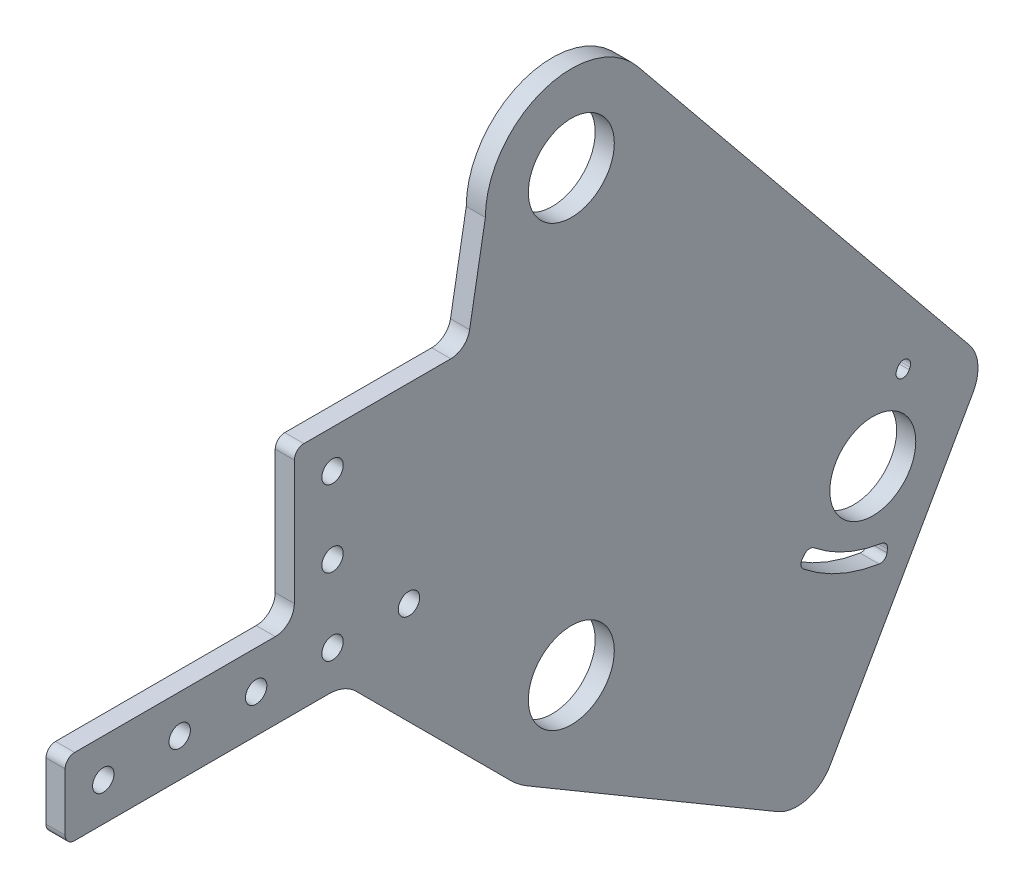
SolidWorks part; units mm, degrees
ref_plane "Front Plane" through (0, 0, 0) normal (0, 0, 1) x (1, 0, 0)
ref_plane "Top Plane" through (0, 0, 0) normal (0, 1, 0) x (1, 0, 0)
ref_plane "Right Plane" through (0, 0, 0) normal (1, 0, 0) x (0, 0, -1)
sketch "Sketch2" plane through (0, 0, 0) normal (1, 0, 0) x (0, 0, -1)
  line L0 (-165.1, 34.925) -> (-80.5967, 34.925)
  line L1 (-14.5065, -24.6189) -> (68.578, -73.576)
  line L2 (-168.275, 38.1) -> (-168.275, 57.15)
  line L3 (-165.1, 60.325) -> (-98.425, 60.325)
  line L4 (-28.575, 146.05) -> (-33.808, 116.3723)
  line L5 (41.6129, 175.1877) -> (218.62, -77.6046) construction
  line L6 (13.9945, 159.0466) -> (128.2067, 36.0649) construction
  line L7 (67.1043, -8.9684) -> (-16.5567, 136.5299) construction
  line L8 (4.3713, 18.5916) -> (87.911, -1.0502) construction
  line L9 (55.482, -68.1997) -> (-11.8433, -14.9831) construction
  line L10 (110.2285, 32.7068) -> (110.4914, 33.3013) construction
  line L11 (83.3117, -13.8327) -> (75.0254, -62.6342) construction
  line L12 (-20.2056, -20.2056) -> (-71.6164, 31.2053)
  line L13 (0, 95.25) -> (255.6229, 95.25) construction
  line L14 (0, 50.8) -> (255.6229, 50.8) construction
  line L15 (133.5362, 14.5746) -> (86.2218, -68.6284)
  line L16 (22.1519, 164.1006) -> (132.3416, 28.875)
  line L17 (108.1378, 33.6314) -> (108.4008, 34.2259)
  line L18 (112.3192, 31.7822) -> (112.5821, 32.3766)
  line L19 (79.2571, -5.4656) -> (78.6197, -6.2567) construction
  line L21 (77.477, -4.0313) -> (76.8396, -4.8225)
  line L22 (102.8251, -15.8889) -> (102.6687, -16.8928) construction
  line L23 (105.0839, -16.2409) -> (104.9274, -17.2448)
  line L26 (110.4914, 33.3013) -> (79.2571, -5.4656) construction
  line L27 (110.4914, 33.3013) -> (102.8251, -15.8889) construction
  line L28 (100.2177, 10.0717) -> (110.4914, 33.3013) construction
  line L29 (-92.075, 66.675) -> (-92.075, 107.95)
  line L30 (-88.9, 111.125) -> (-40.0615, 111.125)
  circle A0 centre (0, 146.05) radius 14.2875
  circle A1 centre (0, 0) radius 14.2875
  circle A2 centre (0, 146.05) radius 50.8 construction
  circle A3 centre (0, 0) radius 50.8 construction
  circle A5 centre (-53.975, 47.625) radius 3.556
  circle A6 centre (-79.375, 47.625) radius 3.556
  circle A7 centre (-104.775, 47.625) radius 3.556
  circle A8 centre (-130.175, 47.625) radius 3.556
  circle A9 centre (-155.575, 47.625) radius 3.556
  arc A10 (22.1519, 164.1006) -> (-28.575, 146.05) centre (0, 146.05) ccw
  arc A11 (-168.275, 57.15) -> (-165.1, 60.325) centre (-165.1, 57.15) cw
  arc A12 (-165.1, 34.925) -> (-168.275, 38.1) centre (-165.1, 38.1) cw
  arc A14 (-71.6164, 31.2053) -> (-80.5967, 34.925) centre (-80.5967, 22.225) ccw
  arc A15 (4.3713, 18.5916) -> (-11.8433, -14.9831) centre (0, 0) ccw construction
  arc A16 (13.9945, 159.0466) -> (-16.5567, 136.5299) centre (0, 146.05) ccw construction
  arc A17 (67.1043, -8.9684) -> (128.2067, 36.0649) centre (100.2177, 10.0717) ccw construction
  arc A18 (55.482, -68.1997) -> (87.911, -1.0502) centre (79.1685, -38.2335) ccw construction
  circle A19 centre (79.1685, -38.2335) radius 32 construction
  circle A20 centre (100.2177, 10.0717) radius 32 construction
  circle A21 centre (100.2177, 10.0717) radius 24.75 construction
  circle A24 centre (79.1685, -38.2335) radius 24.75 construction
  circle A25 centre (83.3117, -13.8327) radius 2.286 construction
  circle A26 centre (75.0254, -62.6342) radius 2.286 construction
  arc A29 (-20.2056, -20.2056) -> (-14.5065, -24.6189) centre (0, 0) ccw
  arc A30 (133.5362, 14.5746) -> (132.3416, 28.875) centre (122.4964, 20.8525) ccw
  arc A31 (68.578, -73.576) -> (86.2218, -68.6284) centre (75.0254, -62.6342) ccw
  circle A32 centre (100.2177, 10.0717) radius 14.2875
  circle A33 centre (79.1685, -38.2335) radius 14.2875 construction
  arc A34 (108.1378, 33.6314) -> (112.3192, 31.7822) centre (110.2285, 32.7068) ccw
  arc A35 (112.5821, 32.3766) -> (108.4008, 34.2259) centre (110.4914, 33.3013) ccw
  arc A37 (76.8396, -4.8225) -> (77.1855, -8.0368) centre (78.6197, -6.2567) ccw
  arc A38 (105.0839, -16.2409) -> (103.1772, -13.6302) centre (102.8251, -15.8889) ccw
  arc A39 (102.3167, -19.1515) -> (104.9274, -17.2448) centre (102.6687, -16.8928) ccw
  arc A40 (80.6914, -3.6854) -> (103.1772, -13.6302) centre (110.4914, 33.3013) ccw
  arc A41 (77.1855, -8.0368) -> (102.3167, -19.1515) centre (110.4914, 33.3013) ccw
  arc A42 (80.6914, -3.6854) -> (77.477, -4.0313) centre (79.2571, -5.4656) ccw
  arc A45 (-92.075, 66.675) -> (-98.425, 60.325) centre (-98.425, 66.675) cw
  arc A46 (-40.0615, 111.125) -> (-33.808, 116.3723) centre (-40.0615, 117.475) ccw
  arc A47 (-92.075, 107.95) -> (-88.9, 111.125) centre (-88.9, 107.95) cw
  circle A48 centre (-79.375, 73.025) radius 3.556
  circle A49 centre (-79.375, 98.425) radius 3.556
  point P50 (110.36, 33.004)
  point P56 (79.1685, -38.2335)
  point P74 (78.9384, -5.8611)
  point P79 (102.7469, -16.3909)
  dimension "D1" = 28.575
  dimension "D2" = 101.6
  dimension "D3" = 44.45
  dimension "D4" = 34.925
  dimension "D6" = 57.15
  dimension "D8" = 7.112
  dimension "D14" = 100
  dimension "D15" = 3.175
  dimension "D16" = 12.7
  dimension "D18" = 38.1972
  dimension "D19" = 76.3944
  dimension "D20" = 520
  dimension "D21" = 360
  dimension "D22" = 64
  dimension "D23" = 49.5
  dimension "D24" = 4.572
  dimension "D25" = 12.7
  dimension "D26" = 28.575
  dimension "D27" = 25.4
  dimension "D28" = 2.286
  dimension "D29" = 1.016
  dimension "D36" = 12.7
  dimension "D37" = 12.7
  dimension "D38" = 25.4
  dimension "D39" = 6.35
  dimension "D40" = 3.175
  dimension "D5" = 135
  dimension "D7" = 12.7
  dimension "D9" = 53.975
  dimension "D10" = 12.7
  dimension "D12" = 25.4
  dimension "D13" = 12.7
  dimension "D17" = 55
  dimension "D30" = 3
  dimension "D31" = 30
  dimension "D32" = 15
  dimension "D33" = 50.8
  dimension "D34" = 50.8
  dimension "D35" = 1.016
  dimension "D11" = 5
extrude "Boss-Extrude1" add sketch "Sketch2" along normal blind 6.35
